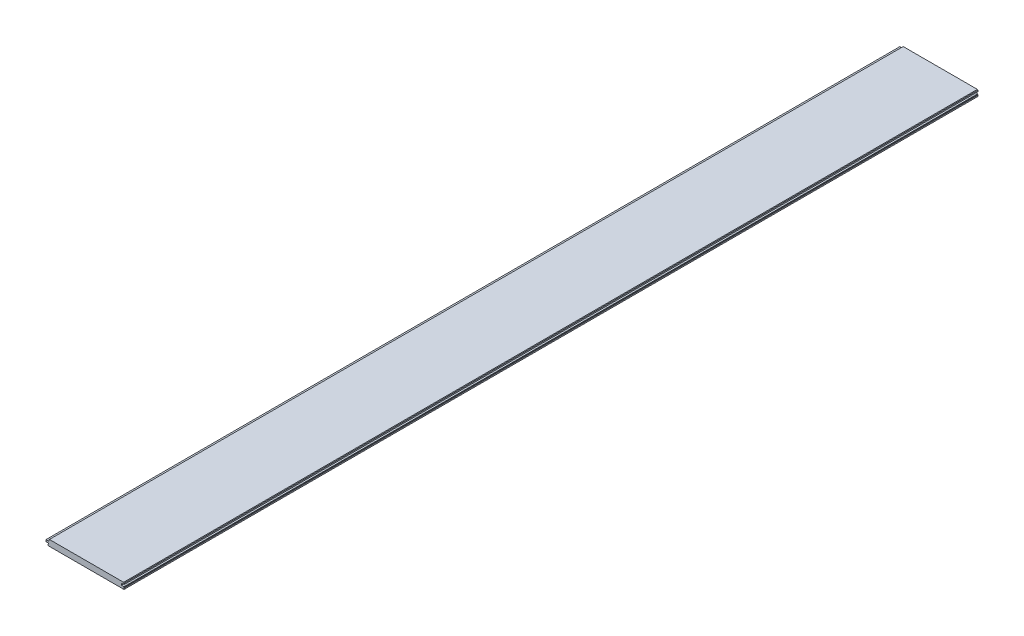
SolidWorks part; units mm, degrees
ref_plane "Front Plane" through (0, 0, 0) normal (0, 0, 1) x (1, 0, 0)
ref_plane "Top Plane" through (0, 0, 0) normal (0, 1, 0) x (1, 0, 0)
ref_plane "Right Plane" through (0, 0, 0) normal (1, 0, 0) x (0, 0, -1)
sketch "Sketch1" plane through (0, 0, 0) normal (0, 0, 1) x (1, 0, 0)
  line L0 (-93.1355, 2.9845) -> (-100.3745, 2.9845)
  line L1 (-95.1675, 7.5565) -> (95.1675, 7.5565)
  line L2 (-95.1675, 7.5565) -> (-95.1675, -7.5565)
  line L3 (-95.1675, -7.5565) -> (95.1675, -7.5565)
  line L4 (95.1675, 7.5565) -> (95.1675, -7.5565)
  line L5 (-95.1675, 7.5565) -> (95.1675, -7.5565) construction
  line L6 (-95.1675, -7.5565) -> (95.1675, 7.5565) construction
  line L7 (-100.3745, 2.9845) -> (-100.3745, -1.5875)
  line L8 (-100.3745, -1.5875) -> (-95.1675, -1.5875)
  line L9 (-95.1675, -1.5875) -> (-95.1675, -7.5565)
  line L10 (94.8372, 3.1242) -> (87.9158, 3.1242)
  line L11 (87.9158, 3.1242) -> (87.9158, -1.4986)
  line L12 (87.9158, -1.4986) -> (94.5324, -1.4986)
  line L13 (94.5324, -1.4986) -> (94.5324, -3.1115)
  line L14 (-93.1355, 2.9845) -> (-93.1355, 7.5565)
  line L15 (-93.1355, 6.2865) -> (-91.8654, 7.5565)
  line L16 (-95.1675, -1.5875) -> (-94.5324, -1.5875)
  line L17 (-94.5324, -1.5875) -> (-94.5324, -3.1115)
  line L18 (-94.5324, -3.1115) -> (-95.1675, -3.7465)
  line L19 (-94.5324, -7.5565) -> (-95.1675, -6.9215)
  line L20 (94.8372, 3.1242) -> (94.8372, 7.5565)
  line L21 (94.5324, -3.1115) -> (95.1675, -3.7465)
  line L22 (94.5324, -7.5565) -> (95.1675, -6.9215)
  line L23 (94.8372, 6.2865) -> (93.5672, 7.5565)
  dimension "D1" = 190.3349
  dimension "D2" = 15.113
  dimension "D3" = 9.144
  dimension "D4" = 7.239
  dimension "D5" = 4.572
  dimension "D6" = 5.207
  dimension "D7" = 6.0579
  dimension "D8" = 4.6228
  dimension "D9" = 0.635
  dimension "D10" = 6.9215
  dimension "D11" = 45
  dimension "D12" = 1.27
  dimension "D13" = 3.81
  dimension "D14" = 0.635
  dimension "D15" = 45
  dimension "D16" = 0.635
  dimension "D17" = 45
  dimension "D18" = 7.2517
  dimension "D19" = 1.27
extrude "Boss-Extrude1" add sketch "Sketch1" along normal mid plane 2133.6 contours L13 L12 L11 L10 L4 L1 L2 L8 L9 L3 | L7 L8 L2 L0
sketch "Sketch2" plane through (0, 0, 0) normal (0, 0, 1) x (1, 0, 0)
  line L0 (-94.5324, -7.5565) -> (94.5325, -7.5565) construction
  line L1 (-94.5324, -7.5565) -> (94.5325, -7.5565)
  point P2 (0, -7.5565)
